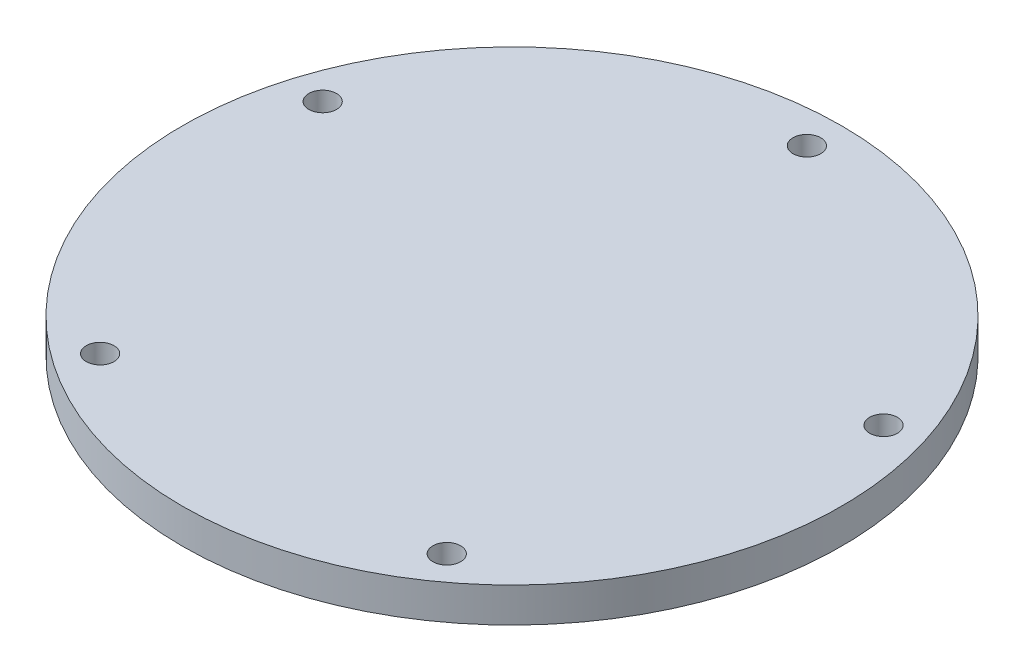
SolidWorks part; units mm, degrees
material "Acrylic (Medium-high impact)"
ref_plane "Front Plane" through (0, 0, 0) normal (0, 0, 1) x (1, 0, 0)
ref_plane "Top Plane" through (0, 0, 0) normal (0, 1, 0) x (1, 0, 0)
ref_plane "Right Plane" through (0, 0, 0) normal (1, 0, 0) x (0, 0, -1)
sketch "Sketch1" plane through (0, 0, 0) normal (0, 1, 0) x (1, 0, 0)
  circle A0 centre (0, 0) radius 47.5
  circle A1 centre (0, 0) radius 42.5 construction
  circle A2 centre (0, 42.5) radius 2
  circle A3 centre (40.4199, 13.1332) radius 2
  circle A4 centre (24.9809, -34.3832) radius 2
  circle A5 centre (-24.9809, -34.3832) radius 2
  circle A6 centre (-40.4199, 13.1332) radius 2
  point P17 (0, 0)
  dimension "D1" = 95
  dimension "D2" = 85
  dimension "D3" = 4
  dimension "D4" = 5
extrude "Boss-Extrude1" add sketch "Sketch1" along normal blind 5
